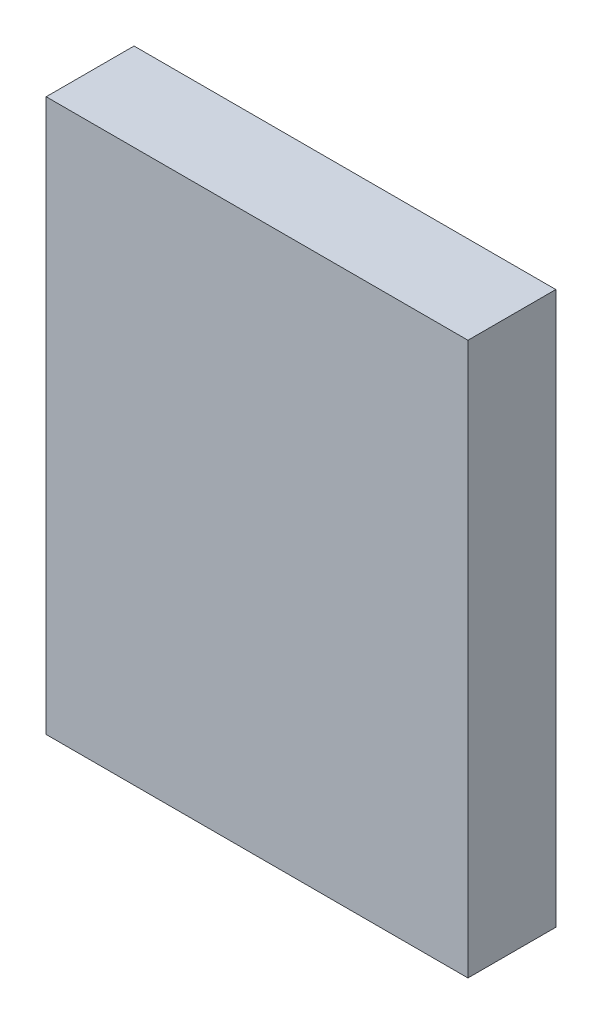
SolidWorks part; units mm, degrees
ref_plane "Front Plane" through (0, 0, 0) normal (0, 0, 1) x (1, 0, 0)
ref_plane "Top Plane" through (0, 0, 0) normal (0, 1, 0) x (1, 0, 0)
ref_plane "Right Plane" through (0, 0, 0) normal (1, 0, 0) x (0, 0, -1)
sketch "Sketch1" plane through (0, 0, 0) normal (0, 0, 1) x (1, 0, 0)
  line L1 (0, 0) -> (213.36, 0)
  line L2 (0, 0) -> (0, 279.4)
  line L3 (0, 279.4) -> (213.36, 279.4)
  line L4 (213.36, 0) -> (213.36, 279.4)
  dimension "D1" = 213.36
  dimension "D2" = 279.4
extrude "Boss-Extrude1" add sketch "Sketch1" along normal blind 44.45
